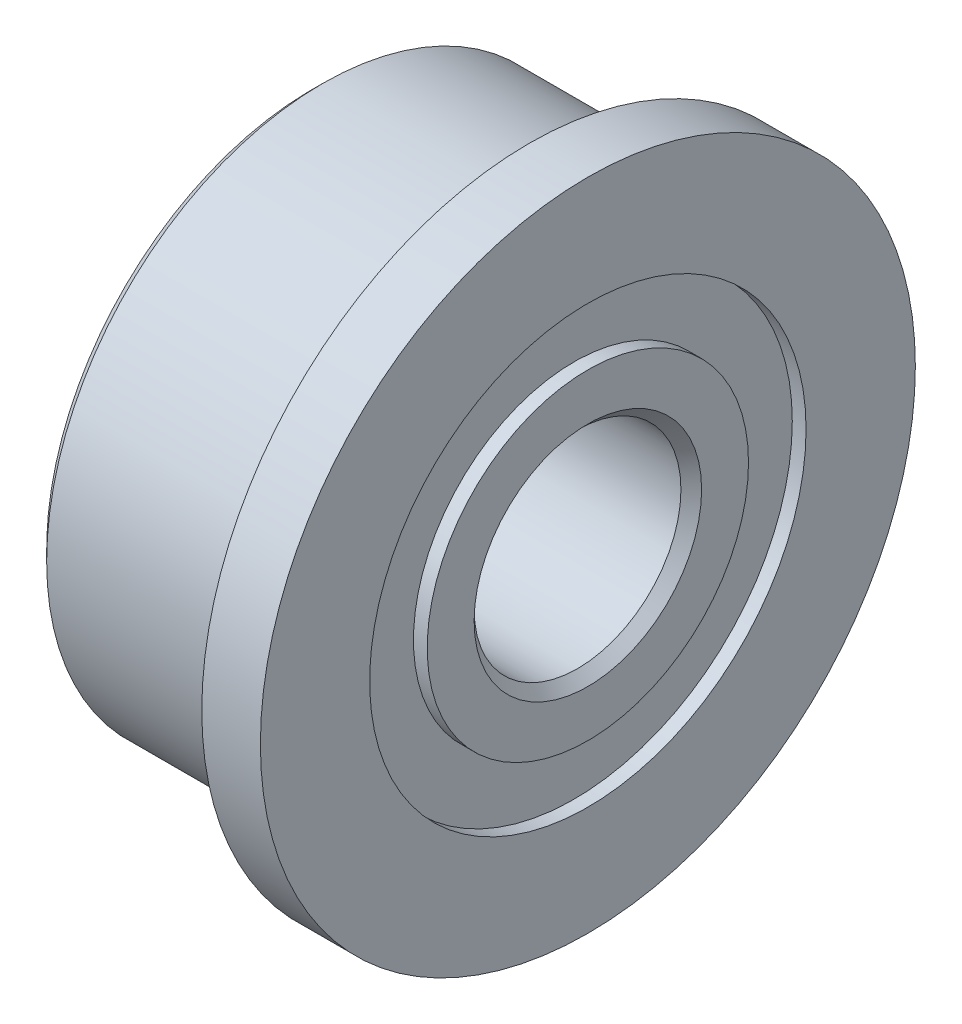
SolidWorks part; units mm, degrees
material "AISI 304"
ref_plane "Piano frontale" through (0, 0, 0) normal (0, 0, 1) x (1, 0, 0)
ref_plane "Piano superiore" through (0, 0, 0) normal (0, 1, 0) x (1, 0, 0)
ref_plane "Piano destro" through (0, 0, 0) normal (1, 0, 0) x (0, 0, -1)
sketch "Schizzo1" plane through (0, 0, 0) normal (0, 0, 1) x (1, 0, 0)
  line L0 (-3.8, 3.165) -> (-3.8, 2.33)
  line L1 (-3.8, 2.33) -> (-4, 2.33)
  line L2 (-4, 2.33) -> (-4, 1.65)
  line L3 (-4, 1.65) -> (-3.85, 1.5)
  line L4 (-3.85, 1.5) -> (-0.15, 1.5)
  line L5 (-0.15, 1.5) -> (0, 1.65)
  line L6 (0, 1.65) -> (0, 2.33)
  line L7 (0, 2.33) -> (-0.2, 2.33)
  line L8 (-0.2, 2.33) -> (-0.2, 3.165)
  line L9 (-0.2, 3.165) -> (0, 3.165)
  line L10 (0, 3.165) -> (0, 4.75)
  line L11 (0, 4.75) -> (-0.85, 4.75)
  line L12 (-0.85, 4.75) -> (-0.85, 4.02)
  line L13 (-0.87, 4) -> (-3.85, 4)
  line L14 (-3.85, 4) -> (-4, 3.85)
  line L15 (-4, 3.85) -> (-4, 3.165)
  line L16 (-4, 3.165) -> (-3.8, 3.165)
  line L17 (-4, 0) -> (0, 0) construction
  arc A0 (-0.85, 4.02) -> (-0.87, 4) centre (-0.85, 4) cw
  dimension "D1" = 0.835
  dimension "D2" = 0.83
  dimension "D3" = 0.835
  dimension "D4" = 1.5
  dimension "D5" = 3.15
  dimension "D6" = 0.85
  dimension "D7" = 1.585
  dimension "D8" = 0.2121
revolve "Rivoluzione1" add sketch "Schizzo1" angle 360 about L17
